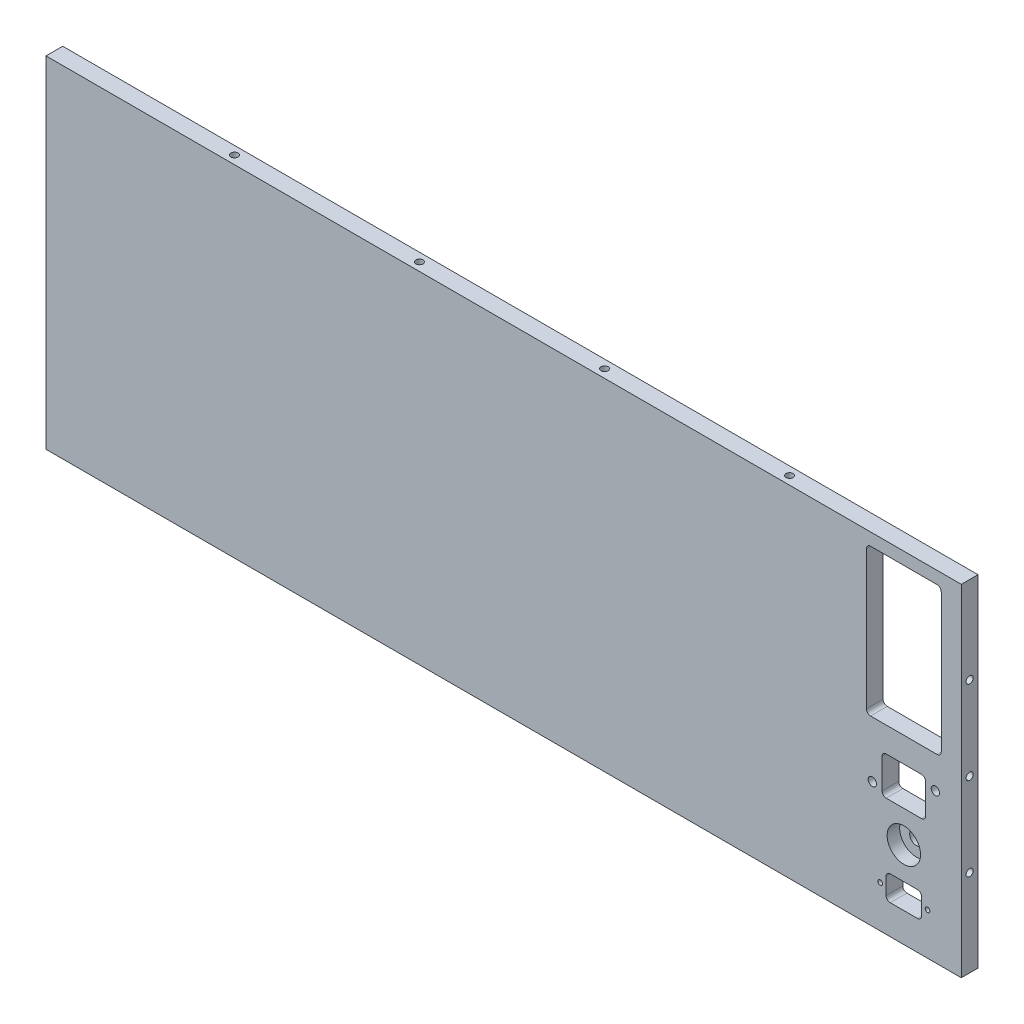
SolidWorks part; units mm, degrees
material "6061 Alloy"
ref_plane "Front Plane" through (0, 0, 0) normal (0, 0, 1) x (1, 0, 0)
ref_plane "Top Plane" through (0, 0, 0) normal (0, 1, 0) x (1, 0, 0)
ref_plane "Right Plane" through (0, 0, 0) normal (1, 0, 0) x (0, 0, -1)
sketch "Sketch1" plane through (0, 0, 0) normal (0, 0, 1) x (1, 0, 0)
  line L1 (0, 0) -> (347.98, 0)
  line L2 (0, 0) -> (0, 129.54)
  line L3 (0, 129.54) -> (347.98, 129.54)
  line L4 (347.98, 0) -> (347.98, 129.54)
  dimension "D1" = 347.98
  dimension "D2" = 129.54
extrude "Boss-Extrude1" add sketch "Sketch1" along normal blind 6.35
hole_wizard "Tap Drill for #6-32 Tap4" positions "Sketch8" profile "Sketch9" hole size "#6-32" standard "ANSI Inch"
sketch "Sketch8" plane through (0, 13.3032, -243.1125) normal (-1, 0, 0) x (0, 0, 1)
  line L1 (243.1125, 51.4668) -> (249.4625, 51.4668) construction
  line L2 (243.1125, 116.2368) -> (243.1125, -13.3032) construction
  line L3 (249.4625, 116.2368) -> (249.4625, -13.3032) construction
  line L5 (246.2875, 116.2368) -> (246.2875, -13.3032) construction
  line L6 (249.4625, 116.2368) -> (243.1125, 116.2368) construction
  line L7 (249.4625, -13.3032) -> (243.1125, -13.3032) construction
  point P0 (-105.5025, 81.9468)
  point P3 (-105.5025, 56.5468)
  point P6 (-105.5025, 31.1468)
  point P9 (246.2875, 83.2168)
  point P12 (246.2875, 51.4668)
  point P15 (246.2875, 19.7168)
  dimension "D2" = 31.75
  dimension "D3" = 31.75
sketch "Sketch9" plane through (0, 95.25, -348.615) normal (0, 1, 0) x (0, 0, 1)
  line L0 (0, 0) -> (0, 18.5927)
  line L1 (0, 18.5927) -> (1.3525, 17.78)
  line L2 (1.3525, 17.78) -> (1.3525, 0)
  line L3 (1.3525, 0) -> (0, 0)
  line L4 (0, 18.5927) -> (-1.3526, 17.78) construction
  line L5 (0, -6.35) -> (0, 107.95) construction
  dimension "Hole Dia." = 2.7051
  dimension "Hole Depth" = 17.78
  dimension "Drill Angle" = 118
sketch "Sketch10" plane through (0, 0, 6.35) normal (0, 0, 1) x (1, 0, 0)
  line L0 (326.136, 68.9356) -> (326.136, 11.6884) construction
  line L1 (313.4995, 124.841) -> (338.7725, 124.841)
  line L2 (311.912, 123.2535) -> (311.912, 70.5231)
  line L3 (313.4995, 68.9356) -> (338.7725, 68.9356)
  line L4 (340.36, 123.2535) -> (340.36, 70.5231)
  line L6 (326.136, 124.841) -> (326.136, 68.9356) construction
  line L7 (331.2985, 20.7064) -> (320.9735, 20.7064)
  line L8 (332.886, 19.1189) -> (332.886, 12.7939)
  line L9 (331.2985, 11.2064) -> (320.9735, 11.2064)
  line L10 (319.386, 19.1189) -> (319.386, 12.7939)
  line L11 (326.136, 68.9356) -> (340.36, 96.8883) construction
  line L12 (340.36, 96.8883) -> (311.912, 96.8883) construction
  line L14 (347.98, 129.54) -> (0, 129.54) construction
  line L15 (335.136, 15.9564) -> (317.136, 15.9564) construction
  line L16 (332.8289, 59.4106) -> (319.4431, 59.4106)
  line L17 (334.4164, 57.8231) -> (334.4164, 46.4439)
  line L18 (332.8289, 44.8564) -> (319.4431, 44.8564)
  line L19 (317.8556, 57.8231) -> (317.8556, 46.4439)
  line L20 (334.4164, 59.4106) -> (317.8556, 44.8564) construction
  line L21 (334.4164, 44.8564) -> (317.8556, 59.4106) construction
  line L22 (334.4164, 52.1335) -> (317.8556, 52.1335) construction
  line L23 (347.98, 0) -> (347.98, 129.54) construction
  circle A0 centre (335.136, 15.9564) radius 0.889
  circle A1 centre (317.136, 15.9564) radius 0.889
  arc A2 (311.912, 70.5231) -> (313.4995, 68.9356) centre (313.4995, 70.5231) ccw
  arc A3 (340.36, 70.5231) -> (338.7725, 68.9356) centre (338.7725, 70.5231) cw
  arc A4 (340.36, 123.2535) -> (338.7725, 124.841) centre (338.7725, 123.2535) ccw
  arc A5 (311.912, 123.2535) -> (313.4995, 124.841) centre (313.4995, 123.2535) cw
  circle A6 centre (338.1248, 56.6293) radius 1.5875
  circle A7 centre (314.1472, 47.6377) radius 1.5875
  arc A8 (319.4431, 44.8564) -> (317.8556, 46.4439) centre (319.4431, 46.4439) cw
  arc A9 (334.4164, 46.4439) -> (332.8289, 44.8564) centre (332.8289, 46.4439) cw
  arc A10 (319.4431, 59.4106) -> (317.8556, 57.8231) centre (319.4431, 57.8231) ccw
  arc A11 (332.8289, 59.4106) -> (334.4164, 57.8231) centre (332.8289, 57.8231) cw
  arc A12 (320.9735, 11.2064) -> (319.386, 12.7939) centre (320.9735, 12.7939) cw
  arc A13 (320.9735, 20.7064) -> (319.386, 19.1189) centre (320.9735, 19.1189) ccw
  arc A14 (331.2985, 20.7064) -> (332.886, 19.1189) centre (331.2985, 19.1189) cw
  arc A15 (332.886, 12.7939) -> (331.2985, 11.2064) centre (331.2985, 12.7939) cw
  circle A16 centre (326.136, 32.7814) radius 2.55
  point P12 (326.136, 52.1335)
  point P22 (340.36, 68.9356)
  point P25 (340.36, 124.841)
  point P28 (311.912, 124.841)
  point P63 (319.386, 20.7064)
  point P66 (332.886, 20.7064)
  point P69 (332.886, 11.2064)
  dimension "D10" = 16.5608
  dimension "D11" = 3.175
  dimension "D12" = 11.9888
  dimension "D13" = 1.5875
  dimension "D15" = 3.175
  dimension "D8" = 14.5542
  dimension "D16" = 9.525
  dimension "D17" = 1.778
  dimension "D18" = 1.778
  dimension "D21" = 1.5875
  dimension "D22" = 1.5875
  dimension "D26" = 5.1
  dimension "D28" = 6.75
  dimension "D1" = 28.448
  dimension "D2" = 55.9054
  dimension "D3" = 9.525
  dimension "D4" = 7.62
  dimension "D5" = 9.5
  dimension "D6" = 13.5
  dimension "D7" = 4.699
  dimension "D9" = 9.525
  dimension "D14" = 11.9888
  dimension "D19" = 9
  dimension "D20" = 9
  dimension "D23" = 4.75
  dimension "D24" = 4.4958
  dimension "D25" = 4.4958
hole_wizard "Tap Drill for #6-32 Tap1" positions "Sketch11" profile "Sketch12" hole size "#6-32" standard "ANSI Inch"
sketch "Sketch11" plane through (-62.9249, 129.54, 269.1876) normal (0, 1, 0) x (0, 0, -1)
  line L0 (266.0126, -62.9249) -> (266.0126, -410.9049) construction
  line L1 (262.8376, -62.9249) -> (269.1876, -62.9249) construction
  line L2 (262.8376, -410.9049) -> (269.1876, -410.9049) construction
  line L3 (266.0126, -410.9049) -> (269.1876, -236.9149) construction
  line L4 (269.1876, -410.9049) -> (269.1876, -62.9249) construction
  line L5 (269.1876, -236.9149) -> (262.8376, -236.9149) construction
  line L6 (262.8376, -410.9049) -> (262.8376, -62.9249) construction
  point P18 (266.0126, -131.3779)
  point P21 (266.0126, -201.7359)
  point P24 (266.0126, -272.0939)
  point P27 (266.0126, -342.4519)
  dimension "D1" = 35.179
  dimension "D2" = 35.179
  dimension "D3" = 70.358
  dimension "D4" = 70.358
sketch "Sketch12" plane through (68.453, 129.54, 3.175) normal (1, 0, 0) x (0, 0, 1)
  line L0 (0, 0) -> (0, 18.5927)
  line L1 (0, 18.5927) -> (1.3525, 17.78)
  line L2 (1.3525, 17.78) -> (1.3525, 0)
  line L3 (1.3525, 0) -> (0, 0)
  line L4 (0, 18.5927) -> (-1.3525, 17.78) construction
  line L5 (0, -6.35) -> (0, 107.95) construction
  dimension "Hole Dia." = 2.7051
  dimension "Hole Depth" = 17.78
  dimension "Drill Angle" = 118
hole_wizard "Tap Drill for #6-32 Tap2" positions "Sketch13" profile "Sketch14" hole size "#6-32" standard "ANSI Inch"
sketch "Sketch13" plane through (-62.9249, 0, 269.1876) normal (0, -1, 0) x (0, 0, 1)
  circle A0 centre (-266.0126, -272.0939) radius 1.3526 construction
  circle A1 centre (-266.0126, -201.7359) radius 1.3526 construction
  circle A2 centre (-266.0126, -131.3779) radius 1.3526 construction
  circle A3 centre (-266.0126, -342.4519) radius 1.3526 construction
  point P18 (-266.0126, -342.4519)
  point P21 (-266.0126, -272.0939)
  point P24 (-266.0126, -201.7359)
  point P27 (-266.0126, -131.3779)
sketch "Sketch14" plane through (279.527, 0, 3.175) normal (1, 0, 0) x (0, 0, -1)
  line L0 (0, 0) -> (0, 18.5927)
  line L1 (0, 18.5927) -> (1.3525, 17.78)
  line L2 (1.3525, 17.78) -> (1.3525, 0)
  line L3 (1.3525, 0) -> (0, 0)
  line L4 (0, 18.5927) -> (-1.3525, 17.78) construction
  line L5 (0, -6.35) -> (0, 107.95) construction
  dimension "Hole Dia." = 2.7051
  dimension "Hole Depth" = 17.78
  dimension "Drill Angle" = 118
extrude "Cut-Extrude1" cut sketch "Sketch10" against normal through all
sketch "Sketch15" plane through (0, 0, 6.35) normal (0, 0, 1) x (1, 0, 0)
  circle A0 centre (326.136, 32.7814) radius 6.35
  dimension "D1" = 12.7
extrude "Cut-Extrude2" cut sketch "Sketch15" against normal blind 4.7625
hole_wizard "Tap Drill for #6-32 Tap5" positions "Sketch17" profile "Sketch16" hole size "#6-32" standard "ANSI Inch"
sketch "Sketch17" plane through (347.98, 0, 0) normal (1, 0, 0) x (0, 0, -1)
  line L1 (-3.175, 129.54) -> (-3.175, 0) construction
  line L4 (-3.175, 0) -> (-6.35, 64.77) construction
  line L5 (-6.35, 0) -> (-6.35, 129.54) construction
  line L6 (-6.35, 64.77) -> (0, 64.77) construction
  line L7 (0, 0) -> (0, 129.54) construction
  line L8 (-6.35, 0) -> (0, 0) construction
  line L9 (-6.35, 129.54) -> (0, 129.54) construction
  point P19 (-3.175, 64.77)
  point P21 (-3.175, 96.52)
  point P23 (-3.175, 33.02)
  dimension "D1" = 31.75
  dimension "D2" = 31.75
sketch "Sketch16" plane through (347.98, 64.77, 3.175) normal (0, 1, 0) x (0, 0, -1)
  line L0 (0, 0) -> (0, 18.5927)
  line L1 (0, 18.5927) -> (1.3525, 17.78)
  line L2 (1.3525, 17.78) -> (1.3525, 0)
  line L5 (1.3525, 0) -> (0, 0)
  line L10 (0, 18.5927) -> (-1.3525, 17.78) construction
  line L11 (0, -6.35) -> (0, 107.95) construction
  dimension "Hole Dia." = 2.7051
  dimension "Hole Depth" = 17.78
  dimension "Drill Angle" = 118
